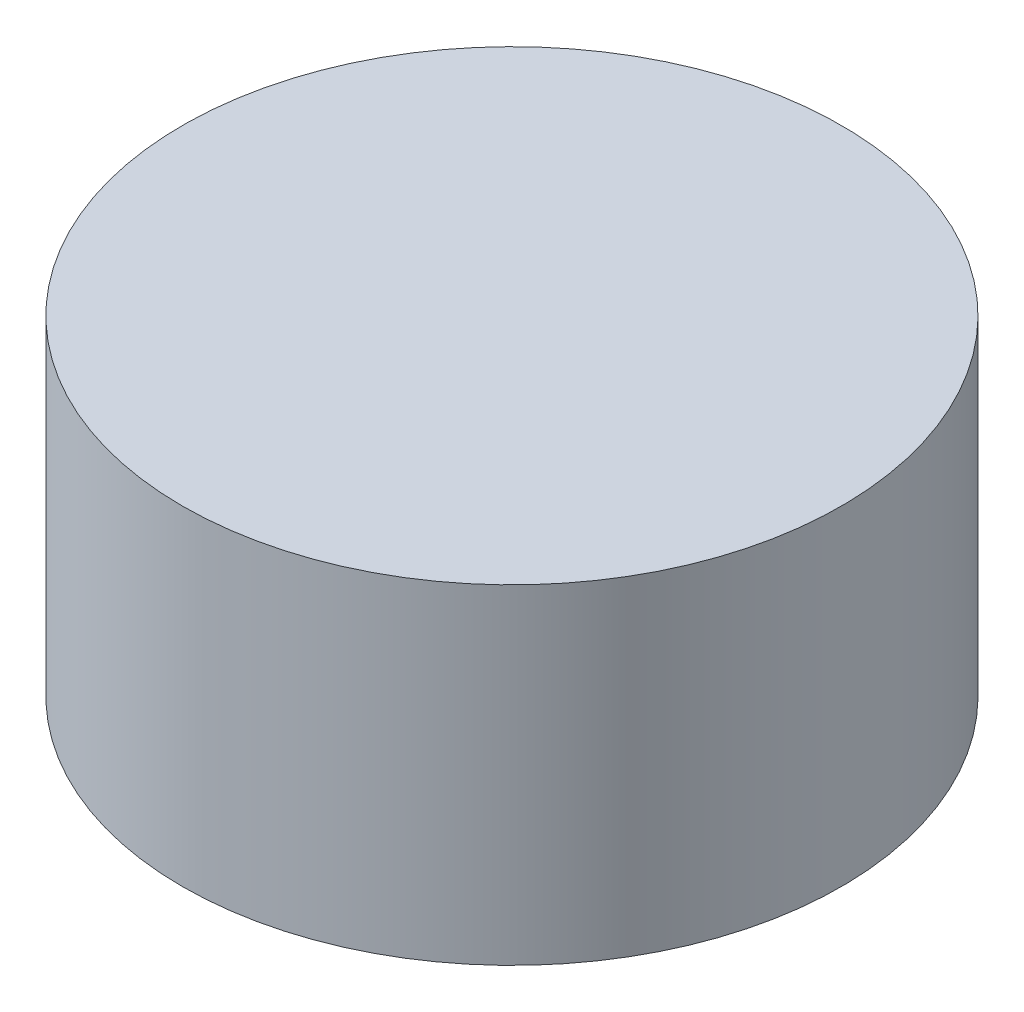
SolidWorks part; units mm, degrees
ref_plane "Front" through (0, 0, 0) normal (0, 0, 1) x (1, 0, 0)
ref_plane "Top" through (0, 0, 0) normal (0, 1, 0) x (1, 0, 0)
ref_plane "Right" through (0, 0, 0) normal (1, 0, 0) x (0, 0, -1)
sketch "Sketch1" plane through (0, 0, 0) normal (0, 1, 0) x (1, 0, 0)
  circle A0 centre (0, 0) radius 8
  dimension "D1" = 16
extrude "Boss-Extrude1" add sketch "Sketch1" along normal blind 8
